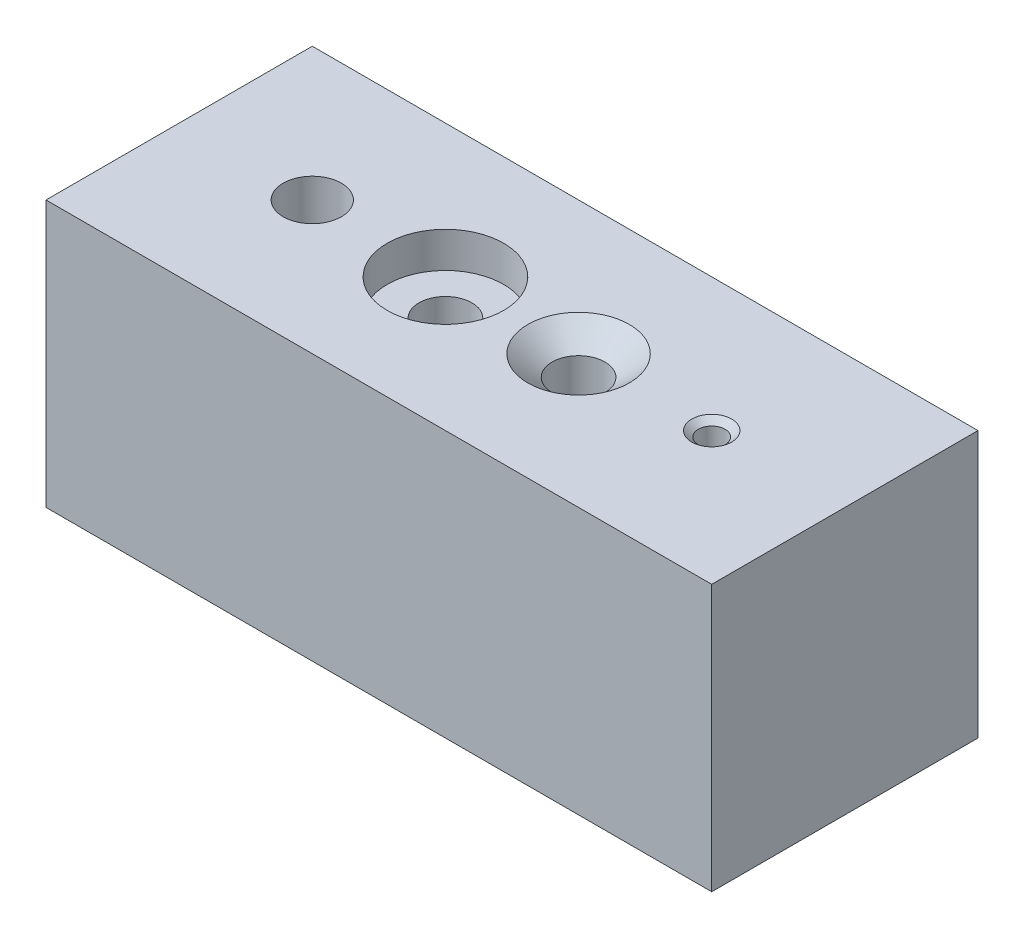
SolidWorks part; units mm, degrees
material "1060 Alloy"
ref_plane "Front Plane" through (0, 0, 0) normal (0, 0, 1) x (1, 0, 0)
ref_plane "Top Plane" through (0, 0, 0) normal (0, 1, 0) x (1, 0, 0)
ref_plane "Right Plane" through (0, 0, 0) normal (1, 0, 0) x (0, 0, -1)
sketch "Sketch1" plane through (0, 0, 0) normal (0, 0, 1) x (1, 0, 0)
  line L1 (-63.5, -25.4) -> (63.5, -25.4)
  line L2 (-63.5, -25.4) -> (-63.5, 25.4)
  line L3 (-63.5, 25.4) -> (63.5, 25.4)
  line L4 (63.5, -25.4) -> (63.5, 25.4)
  line L5 (-63.5, -25.4) -> (63.5, 25.4) construction
  line L6 (-63.5, 25.4) -> (63.5, -25.4) construction
  point P0 (0, 0)
  dimension "D1" = 63.5
  dimension "D2" = 25.4
extrude "Boss-Extrude1" add sketch "Sketch1" along normal blind 50.8
hole_wizard "7/16 (0.4375) Diameter Hole2" positions "3DSketch2" profile "Sketch6" hole size "7/16" standard "ANSI Inch"
sketch3d "3DSketch2"
  line L0 (63.5, 25.4, 0) -> (-63.5, 25.4, 0) construction
  line L1 (-63.5, 25.4, 50.8) -> (-63.5, 25.4, 0) construction
  point P0 (-38.1, 25.4, 25.4)
  dimension "D1" = 25.4
  dimension "D2" = 25.4
sketch "Sketch6" plane through (-38.1, 25.4, 25.4) normal (1, 0, 0) x (0, 0, 1)
  line L0 (0, 0) -> (0, 22.3885)
  line L1 (0, 22.3885) -> (5.5562, 19.05)
  line L2 (5.5562, 19.05) -> (5.5562, 0)
  line L5 (5.5562, 0) -> (0, 0)
  line L10 (0, 22.3885) -> (-5.5562, 19.05) construction
  line L11 (0, -6.35) -> (0, 107.95) construction
  dimension "Hole Dia." = 11.1125
  dimension "Hole Depth" = 19.05
  dimension "Drill Angle" = 118
hole_wizard "CBORE for 3/8 Hex Head Bolt1" positions "3DSketch3" profile "Sketch7" counterbore size "3/8" standard "ANSI Inch" end condition through all
sketch3d "3DSketch3"
  line L0 (63.5, 25.4, 0) -> (-63.5, 25.4, 0) construction
  line L1 (-63.5, 25.4, 50.8) -> (-63.5, 25.4, 0) construction
  point P0 (-12.7, 25.4, 25.4)
  point P12 (0, 0, 0)
  point P13 (0, 0, 0)
  point P14 (0, 0, 0)
  dimension "D2" = 50.8
  dimension "D1" = 25.4
sketch "Sketch7" plane through (-12.7, 25.4, 25.4) normal (1, 0, 0) x (0, 0, 1)
  line L0 (0, 0) -> (0, 50.8)
  line L1 (0, 50.8) -> (5.0419, 50.8)
  line L3 (5.0419, 50.8) -> (5.0419, 6.8072)
  line L4 (5.0419, 6.8072) -> (11.1125, 6.8072)
  line L5 (11.1125, 6.8072) -> (11.1125, 0)
  line L7 (11.1125, 0) -> (0, 0)
  line L11 (0, -6.35) -> (0, 107.95) construction
  dimension "Thru Hole Dia." = 10.0838
  dimension "Thru Hole Depth" = 50.8
  dimension "C'Bore Dia." = 22.225
  dimension "C'Bore Depth" = 6.8072
hole_wizard "CSK for 3/8 Flat Head Machine Screw (100)1" positions "3DSketch4" profile "Sketch8" countersink size "3/8" standard "ANSI Inch"
sketch3d "3DSketch4"
  line L0 (63.5, 25.4, 0) -> (-63.5, 25.4, 0) construction
  line L1 (-63.5, 25.4, 50.8) -> (-63.5, 25.4, 0) construction
  point P0 (12.7, 25.4, 25.4)
  dimension "D1" = 25.4
  dimension "D2" = 76.2
sketch "Sketch8" plane through (12.7, 25.4, 25.4) normal (1, 0, 0) x (0, 0, 1)
  line L0 (0, 0) -> (0, 41.1295)
  line L1 (0, 41.1295) -> (5.0419, 38.1)
  line L2 (5.0419, 38.1) -> (5.0419, 3.8896)
  line L3 (5.0419, 3.8896) -> (9.6774, 0)
  line L5 (9.6774, 0) -> (0, 0)
  line L6 (-5.0419, 3.8896) -> (-9.6774, 0) construction
  line L10 (0, 41.1295) -> (-5.0419, 38.1) construction
  line L11 (0, -6.35) -> (0, 107.95) construction
  dimension "Hole Dia." = 10.0838
  dimension "Hole Depth" = 38.1
  dimension "Near C'Sink Dia." = 19.3548
  dimension "Near C'Sink Angle" = 100
  dimension "Drill Angle" = 118
hole_wizard "1/4-20 Tapped Hole1" positions "3DSketch5" profile "Sketch9" tap size "1/4-20" standard "ANSI Inch"
sketch3d "3DSketch5"
  line L0 (63.5, 25.4, 0) -> (-63.5, 25.4, 0) construction
  line L1 (-63.5, 25.4, 50.8) -> (-63.5, 25.4, 0) construction
  point P0 (38.1, 25.4, 25.4)
  dimension "D1" = 25.4
  dimension "D2" = 101.6
sketch "Sketch9" plane through (38.1, 25.4, 25.4) normal (1, 0, 0) x (0, 0, 1)
  line L0 (0, 0) -> (0, 26.9338)
  line L1 (0, 26.9338) -> (2.5527, 25.4)
  line L2 (2.5527, 25.4) -> (2.5527, 1.055)
  line L3 (2.5527, 1.055) -> (3.81, 0)
  line L5 (3.81, 0) -> (0, 0)
  line L6 (-2.5527, 1.055) -> (-3.81, 0) construction
  line L10 (0, 26.9338) -> (-2.5527, 25.4) construction
  line L11 (0, -6.35) -> (0, 107.95) construction
  dimension "Tap Drill Dia." = 5.1054
  dimension "Tap Drill Depth" = 25.4
  dimension "Near C'Sink Dia." = 7.62
  dimension "Near C'Sink Angle" = 100
  dimension "Drill Angle" = 118
cosmetic thread "Hole Thread1" parameters "D1"=12.7, "D2"=6.35
